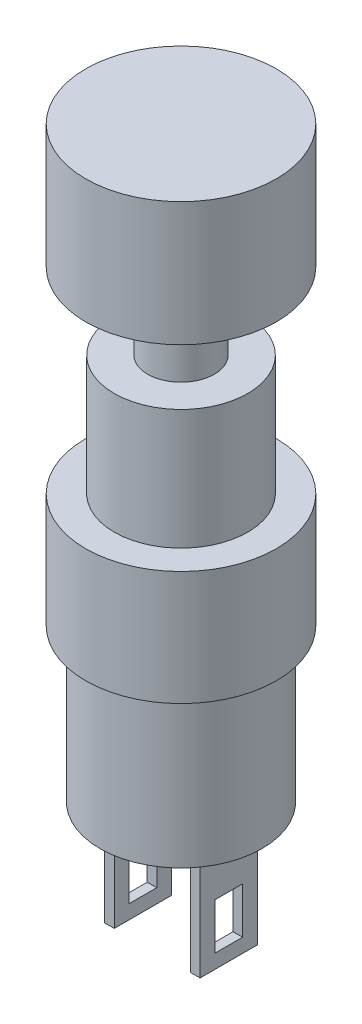
SolidWorks part; units mm, degrees
ref_plane "Plano frontal" through (0, 0, 0) normal (0, 0, 1) x (1, 0, 0)
ref_plane "Plano superior" through (0, 0, 0) normal (0, 1, 0) x (1, 0, 0)
ref_plane "Plano direito" through (0, 0, 0) normal (1, 0, 0) x (0, 0, -1)
sketch "Esboço1" plane through (0, 0, 0) normal (0, 1, 0) x (1, 0, 0)
  circle A0 centre (0, 0) radius 5
  dimension "D1" = 10
extrude "Ressalto-extrusão1" add sketch "Esboço1" along normal blind 6
sketch "Esboço2" plane through (0, 0, 0) normal (0, -1, 0) x (1, 0, 0)
  circle A0 centre (0, 0) radius 4.25
  dimension "D1" = 8.5
extrude "Ressalto-extrusão2" add sketch "Esboço2" along normal blind 8
sketch "Esboço3" plane through (0, -8, 0) normal (0, -1, 0) x (1, 0, 0)
  line L0 (0, 4.25) -> (0, -4.25) construction
  line L1 (0, 0) -> (4.25, 0) construction
  line L2 (2, -1.5) -> (2.5, -1.5)
  line L3 (2, -1.5) -> (2, 1.5)
  line L4 (2, 1.5) -> (2.5, 1.5)
  line L5 (2.5, -1.5) -> (2.5, 1.5)
  line L6 (2, -1.5) -> (2.5, 1.5) construction
  line L7 (2, 1.5) -> (2.5, -1.5) construction
  line L8 (-2, 1.5) -> (-2.5, -1.5) construction
  line L9 (-2, -1.5) -> (-2.5, 1.5) construction
  line L10 (-2.5, -1.5) -> (-2.5, 1.5)
  line L11 (-2, 1.5) -> (-2.5, 1.5)
  line L12 (-2, -1.5) -> (-2, 1.5)
  line L13 (-2, -1.5) -> (-2.5, -1.5)
  circle A0 centre (0, 0) radius 4.25 construction
  circle A1 centre (0, 0) radius 4.25 construction
  point P7 (2.25, 0)
  point P19 (-2.25, 0)
  dimension "D1" = 0.5
  dimension "D2" = 3
  dimension "D3" = 4.5
extrude "Ressalto-extrusão3" add sketch "Esboço3" along normal blind 6
sketch "Esboço4" plane through (-2.5, 0, 0) normal (-1, 0, 0) x (0, 0, 1)
  line L1 (-0.7286, -13.2622) -> (0.7144, -13.2622)
  line L2 (-0.7286, -13.2622) -> (-0.7286, -10.8387)
  line L3 (-0.7286, -10.8387) -> (0.7144, -10.8387)
  line L4 (0.7144, -13.2622) -> (0.7144, -10.8387)
extrude "Corte-extrusão1" cut sketch "Esboço4" against normal through all
sketch "Esboço5" plane through (0, 6, 0) normal (0, 1, 0) x (1, 0, 0)
  circle A0 centre (0, 0) radius 3.5
  dimension "D1" = 7
extrude "Ressalto-extrusão4" add sketch "Esboço5" along normal blind 6.3
sketch "Esboço6" plane through (0, 12.3, 0) normal (0, 1, 0) x (1, 0, 0)
  circle A0 centre (0, 0) radius 1.75
  dimension "D1" = 3.5
extrude "Ressalto-extrusão5" add sketch "Esboço6" along normal blind 4
sketch "Esboço7" plane through (0, 16.3, 0) normal (0, 1, 0) x (1, 0, 0)
  circle A0 centre (0, 0) radius 5
  dimension "D1" = 10
extrude "Ressalto-extrusão6" add sketch "Esboço7" along normal blind 6.5
